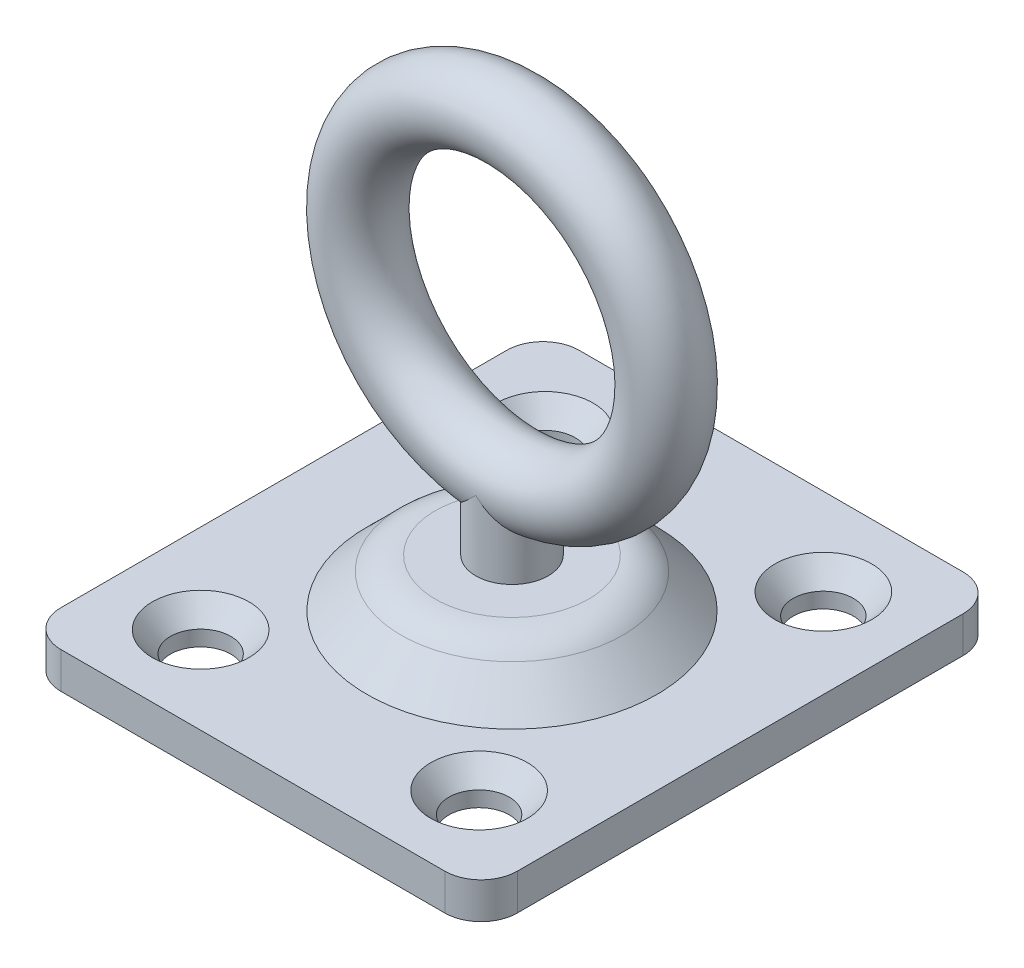
SolidWorks part; units mm, degrees
material "Alloy Steel"
ref_plane "Front Plane" through (0, 0, 0) normal (0, 0, 1) x (1, 0, 0)
ref_plane "Top Plane" through (0, 0, 0) normal (0, 1, 0) x (1, 0, 0)
ref_plane "Right Plane" through (0, 0, 0) normal (1, 0, 0) x (0, 0, -1)
sketch "Sketch1" plane through (0, 0, 0) normal (0, 1, 0) x (1, 0, 0)
  line L0 (0, 17.018) -> (0, -17.018) construction
  line L1 (-12.6047, 17.018) -> (12.6047, 17.018)
  line L2 (-14.986, 14.6367) -> (-14.986, -14.6367)
  line L3 (-12.6047, -17.018) -> (12.6047, -17.018)
  line L4 (14.986, 14.6367) -> (14.986, -14.6367)
  line L5 (-14.986, 0) -> (14.986, 0) construction
  line L7 (-9.144, 11.303) -> (9.144, 11.303) construction
  line L8 (-9.144, 11.303) -> (-9.144, -11.303) construction
  line L9 (-9.144, -11.303) -> (9.144, -11.303) construction
  line L10 (9.144, 11.303) -> (9.144, -11.303) construction
  circle A0 centre (-9.144, 11.303) radius 1.9844 construction
  circle A1 centre (9.144, 11.303) radius 1.9844 construction
  circle A2 centre (9.144, -11.303) radius 1.9844 construction
  circle A3 centre (-9.144, -11.303) radius 1.9844 construction
  arc A4 (-12.6047, 17.018) -> (-14.986, 14.6367) centre (-12.6048, 14.6367) ccw
  arc A5 (12.6047, 17.018) -> (14.986, 14.6367) centre (12.6048, 14.6367) cw
  arc A6 (12.6047, -17.018) -> (14.986, -14.6367) centre (12.6048, -14.6367) ccw
  arc A7 (-14.986, -14.6367) -> (-12.6047, -17.018) centre (-12.6047, -14.6368) ccw
  point P12 (0, 11.303)
  point P13 (-9.144, 0)
  dimension "D5" = 3.9688
  dimension "D6" = 2.3813
  dimension "D1" = 34.036
  dimension "D2" = 29.972
  dimension "D3" = 22.606
  dimension "D4" = 18.288
extrude "Boss-Extrude1" add sketch "Sketch1" along normal blind 2.3813
sketch "Sketch2" plane through (0, 0, 0) normal (0, 1, 0) x (1, 0, 0)
  circle A0 centre (-9.144, 11.303) radius 1.9844 construction
  circle A1 centre (9.144, 11.303) radius 1.9844 construction
  circle A2 centre (9.144, -11.303) radius 1.9844 construction
  circle A3 centre (-9.144, -11.303) radius 1.9844 construction
  circle A4 centre (-9.144, 11.303) radius 1.9844
  circle A5 centre (9.144, 11.303) radius 1.9844
  circle A6 centre (9.144, -11.303) radius 1.9844
  circle A7 centre (-9.144, -11.303) radius 1.9844
extrude "Cut-Extrude1" cut sketch "Sketch2" along normal up to next
sketch "Sketch3" plane through (0, 2.3813, 0) normal (0, 1, 0) x (1, 0, 0)
  circle A0 centre (-9.144, 11.303) radius 3.175
  circle A1 centre (9.144, 11.303) radius 3.175
  circle A2 centre (9.144, -11.303) radius 3.175
  circle A3 centre (-9.144, -11.303) radius 3.175
  dimension "D1" = 6.35
extrude "Cut-Extrude2" cut sketch "Sketch3" against normal through all draft 41
sketch "Sketch4" plane through (0, 0, 0) normal (0, 0, 1) x (1, 0, 0)
  line L0 (0, 0) -> (0, 32.766) construction
  line L1 (0, 28.0035) -> (0, 32.766) construction
  line L2 (-9.525, 2.3812) -> (-7.2799, 4.6263)
  line L3 (-12.6047, 2.3813) -> (12.6047, 2.3813) construction
  line L4 (-5.0349, 5.5562) -> (0, 5.5562)
  line L5 (0, 5.5562) -> (0, 2.3813)
  line L6 (0, 2.3813) -> (-9.525, 2.3812)
  circle A0 centre (0, 20.2565) radius 12.5095 construction
  circle A1 centre (0, 20.2565) radius 7.747 construction
  circle A2 centre (0, 30.3847) radius 2.3813 construction
  arc A3 (-7.2799, 4.6263) -> (-5.0349, 5.5562) centre (-5.0349, 2.3812) cw
  point P17 (-6.35, 5.5562)
  dimension "D1" = 15.494
  dimension "D3" = 4.7625
  dimension "D7" = 3.175
  dimension "D2" = 32.766
  dimension "D4" = 19.05
  dimension "D5" = 12.7
  dimension "D6" = 3.175
revolve "Revolve1" add sketch "Sketch4" angle 360 mid plane about L0
sketch "Sketch5" plane through (0, 0, 0) normal (0, 0, 1) x (1, 0, 0)
  line L0 (0, 32.766) -> (0, 0) construction
  line L1 (0, 5.5562) -> (-2.3813, 5.5562)
  line L2 (-2.3813, 5.5562) -> (-2.3813, 3.175)
  line L3 (-2.3813, 5.5562) -> (-2.3813, 30.3847) construction
  line L4 (0, 30.3847) -> (-2.3813, 30.3847) construction
  line L5 (14.986, 2.3813) -> (14.986, 0) construction
  line L6 (-2.3813, 3.175) -> (-5.0349, 3.175)
  line L7 (-5.5961, 2.9425) -> (-7.8412, 0.6975)
  line L8 (-9.525, 2.3812) -> (-7.2799, 4.6263) construction
  line L10 (0, 0) -> (-9.525, 0)
  line L11 (0, 0) -> (0, 5.5562)
  circle A1 centre (0, 30.3847) radius 2.3813 construction
  arc A2 (-5.0349, 3.175) -> (-5.5961, 2.9425) centre (-5.0349, 2.3812) ccw
  arc A3 (-9.525, 0) -> (-7.8412, 0.6975) centre (-9.525, 2.3813) ccw
revolve "Cut-Revolve1" cut sketch "Sketch5" angle 360 mid plane about L0
sketch "Sketch6" plane through (0, 3.175, 0) normal (0, -1, 0) x (1, 0, 0)
  circle A0 centre (0, 0) radius 2.3813 construction
  circle A1 centre (0, 0) radius 2.3813
  circle A2 centre (0, 0) radius 4.7625
  dimension "D1" = 9.525
extrude "Boss-Extrude2" add sketch "Sketch6" along normal blind 1.1906 separate body
sketch "Sketch7" plane through (0, 0, 0) normal (0, 0, 1) x (1, 0, 0)
  line L0 (0, 32.766) -> (0, 0) construction
  line L1 (-2.3813, 10.1282) -> (-2.3813, 1.9844)
  line L2 (-2.3813, 5.5562) -> (-2.3813, 30.3847) construction
  line L3 (0, 12.5095) -> (0, 7.747) construction
  line L4 (-2.3813, 10.1282) -> (0, 10.1282)
  line L5 (-2.3813, 1.9844) -> (-3.175, 1.9844)
  line L6 (0, 10.1282) -> (0, 0.7937)
  circle A0 centre (0, 20.2565) radius 7.747 construction
  circle A1 centre (0, 20.2565) radius 12.5095 construction
  arc A2 (-3.175, 1.9844) -> (0, 0.7937) centre (0, 5.6224) ccw
  dimension "D1" = 1.1906
  dimension "D2" = 6.35
revolve "Revolve2" add sketch "Sketch7" angle 360 mid plane about L0
sketch "Sketch8" plane through (0, 0, 0) normal (0, 0, 1) x (1, 0, 0)
  circle A0 centre (0, 20.2565) radius 10.1283
sketch "Sketch9" plane through (0, 0, 0) normal (1, 0, 0) x (0, 0, -1)
  line L0 (0, 32.766) -> (0, 28.0035) construction
  circle A0 centre (0, 30.3847) radius 2.3813
sweep "Sweep1" add profiles "Sketch9" path "Sketch8"
